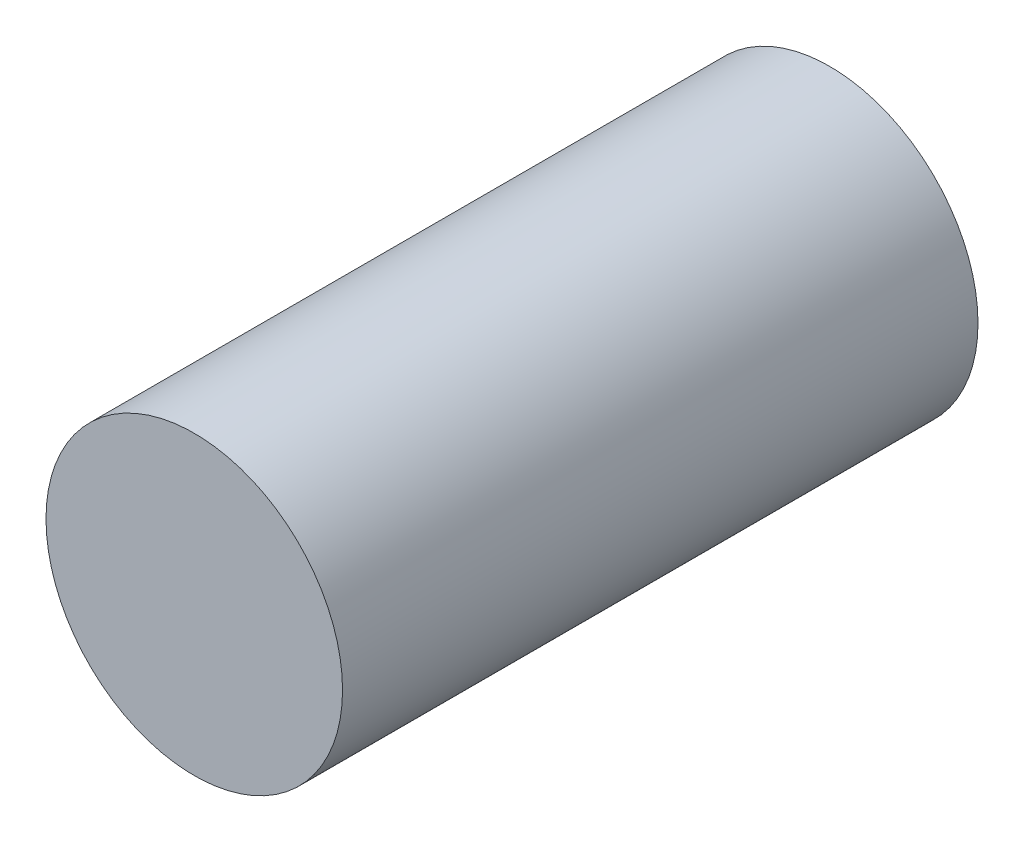
SolidWorks part; units mm, degrees
ref_plane "Front Plane" through (0, 0, 0) normal (0, 0, 1) x (1, 0, 0)
ref_plane "Top Plane" through (0, 0, 0) normal (0, 1, 0) x (1, 0, 0)
ref_plane "Right Plane" through (0, 0, 0) normal (1, 0, 0) x (0, 0, -1)
sketch "Sketch1" plane through (0, 0, 0) normal (0, 0, 1) x (1, 0, 0)
  circle A0 centre (0, 0) radius 3.556
  dimension "D1" = 7.112
extrude "Boss-Extrude1" add sketch "Sketch1" along normal blind 15.24
